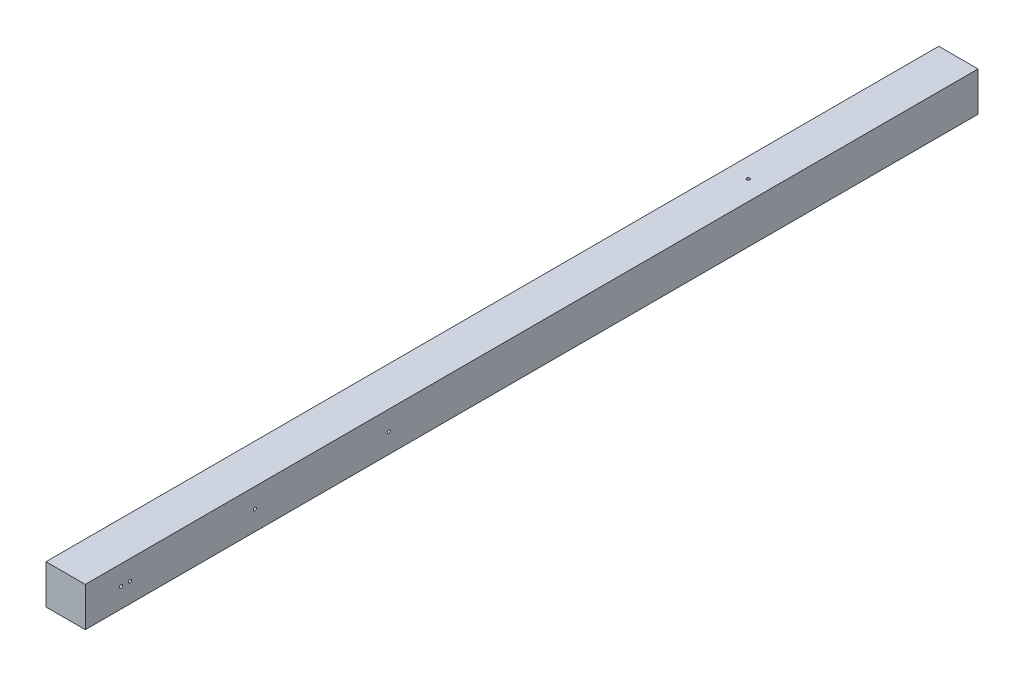
SolidWorks part; units mm, degrees
material "Pin"
ref_plane "Plan de face" through (0, 0, 0) normal (0, 0, 1) x (1, 0, 0)
ref_plane "Plan de dessus" through (0, 0, 0) normal (0, 1, 0) x (1, 0, 0)
ref_plane "Plan de droite" through (0, 0, 0) normal (1, 0, 0) x (0, 0, -1)
sketch "Esquisse1" plane through (0, 0, 0) normal (0, 0, 1) x (1, 0, 0)
  line L1 (22, 22) -> (-22, 22)
  line L2 (22, 22) -> (22, -22)
  line L3 (22, -22) -> (-22, -22)
  line L4 (-22, 22) -> (-22, -22)
  line L5 (22, 22) -> (-22, -22) construction
  line L6 (22, -22) -> (-22, 22) construction
  point P0 (0, 0)
  dimension "D1" = 44
  dimension "D2" = 44
extrude "Boss.-Extru.1" add sketch "Esquisse1" along normal blind 1000
sketch "Esquisse2" plane through (-22, 0, 0) normal (-1, 0, 0) x (0, 0, 1)
  line L0 (1000, 22) -> (1000, -22) construction
  line L1 (1000, -22) -> (0, -22) construction
  circle A0 centre (950, 0) radius 1.75
  circle A1 centre (960, 0) radius 1.75
  circle A2 centre (810, 0) radius 1.75
  circle A3 centre (660, 0) radius 1.75
  dimension "D3" = 3.5
  dimension "D4" = 3.5
  dimension "D5" = 22
  dimension "D6" = 40
  dimension "D1" = 50
  dimension "D2" = 22
  dimension "D7" = 3
extrude "Enlèv. mat.-Extru.1" cut sketch "Esquisse2" against normal up to surface (44 mm away) up to face at (22, 0, 500)
sketch "Esquisse3" plane through (0, 22, 0) normal (0, 1, 0) x (1, 0, 0)
  line L0 (22, 0) -> (-22, 0) construction
  line L1 (-22, -1000) -> (-22, 0) construction
  circle A0 centre (0, -235.31) radius 1.75
  dimension "D1" = 3.5
  dimension "D3" = 22
  dimension "D2" = 235.31
extrude "Enlèv. mat.-Extru.2" cut sketch "Esquisse3" against normal up to surface (44 mm away) up to face at (0, -22, 500)
